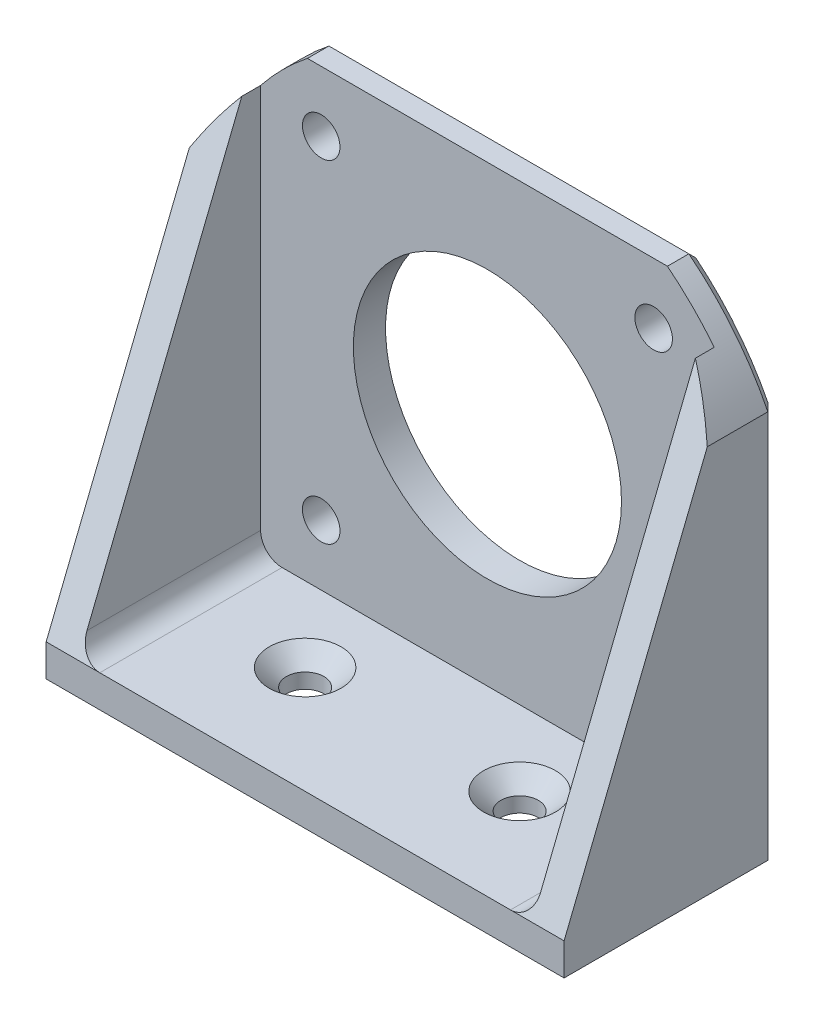
SolidWorks part; units mm, degrees
ref_plane "Front Plane" through (0, 0, 0) normal (0, 0, 1) x (1, 0, 0)
ref_plane "Top Plane" through (0, 0, 0) normal (0, 1, 0) x (1, 0, 0)
ref_plane "Right Plane" through (0, 0, 0) normal (1, 0, 0) x (0, 0, -1)
sketch "Sketch1" plane through (0, 0, 0) normal (0, 1, 0) x (1, 0, 0)
  line L1 (-21.15, 10) -> (21.15, 10) construction
  line L2 (-21.15, 10) -> (-21.15, -10) construction
  line L3 (-21.15, -10) -> (21.15, -10) construction
  line L4 (21.15, 10) -> (21.15, -10) construction
  line L5 (-21.15, 10) -> (21.15, -10) construction
  line L6 (-21.15, -10) -> (21.15, 10) construction
  line L7 (-24.15, 10) -> (24.15, 10)
  line L8 (-24.15, 10) -> (-24.15, -10)
  line L9 (-24.15, -10) -> (24.15, -10)
  line L10 (24.15, 10) -> (24.15, -10)
  line L11 (-24.15, 10) -> (24.15, -10) construction
  line L12 (-24.15, -10) -> (24.15, 10) construction
  point P0 (0, 0)
  point P5 (0, 0)
  dimension "D1" = 20
  dimension "D2" = 42.3
  dimension "D4" = 3
extrude "Boss-Extrude1" add sketch "Sketch1" along normal blind 3
sketch "Sketch2" plane through (0, 3, 0) normal (0, 1, 0) x (1, 0, 0)
  line L0 (24.15, -10) -> (24.15, 10) construction
  line L1 (-24.15, 10) -> (24.15, 10)
  line L2 (-24.15, 10) -> (-24.15, 7)
  line L3 (-24.15, 7) -> (24.15, 7)
  line L4 (24.15, 10) -> (24.15, 7)
  dimension "D1" = 3
extrude "Boss-Extrude2" add sketch "Sketch2" along normal blind 42.3
sketch "Sketch3" plane through (0, 0, -7) normal (0, 0, 1) x (1, 0, 0)
  line L0 (-24.15, 24.15) -> (24.15, 24.15) construction
  line L1 (-24.15, 45.3) -> (-24.15, 3) construction
  line L2 (24.15, 45.3) -> (24.15, 3) construction
  line L4 (-15.5, 39.65) -> (15.5, 39.65) construction
  line L5 (-15.5, 39.65) -> (-15.5, 8.65) construction
  line L6 (-15.5, 8.65) -> (15.5, 8.65) construction
  line L7 (15.5, 39.65) -> (15.5, 8.65) construction
  line L8 (-15.5, 39.65) -> (15.5, 8.65) construction
  line L9 (-15.5, 8.65) -> (15.5, 39.65) construction
  circle A0 centre (0, 24.15) radius 12.5
  circle A1 centre (-15.5, 39.65) radius 1.75
  circle A2 centre (15.5, 39.65) radius 1.75
  circle A3 centre (15.5, 8.65) radius 1.75
  circle A4 centre (-15.5, 8.65) radius 1.75
  point P8 (0, 0)
  point P10 (-15.7944, 8.3556)
  point P11 (0, 0)
  point P13 (0, 0)
  point P14 (0, 0)
  point P22 (0, 24.15)
  dimension "D1" = 25
  dimension "D2" = 3.5
  dimension "D3" = 4
  dimension "D4" = 31
extrude "Cut-Extrude1" cut sketch "Sketch3" against normal through all
sketch "Sketch4" plane through (-24.15, 0, 0) normal (-1, 0, 0) x (0, 0, 1)
  line L0 (-7, 45.3) -> (10, 3)
rib "Rib1" sketch "Sketch4" sketch "Sketch4" thickness 3 extrusion direction parallel to sketch draft on no parameters "D1"=3
mirror "Mirror1" about plane through (0, 0, 0) normal (1, 0, 0) of "Rib1"
sketch "Sketch5" plane through (0, 0, -10) normal (0, 0, -1) x (-1, 0, 0)
  line L0 (-27, 24.15) -> (27, 24.15) construction
  line L1 (-27, 24.15) -> (-32.1021, 24.15)
  line L2 (27, 24.15) -> (32.1021, 24.15)
  arc A0 (27, 24.15) -> (-27, 24.15) centre (0, 24.15) ccw
  arc A1 (32.1021, 24.15) -> (-32.1021, 24.15) centre (0, 24.15) ccw
  dimension "D1" = 54
extrude "Cut-Extrude2" cut sketch "Sketch5" against normal through all
sketch "Sketch6" plane through (0, 3, 0) normal (0, 1, 0) x (1, 0, 0)
  line L0 (-10, -10) -> (-10, 10) construction
  line L1 (-21.15, -10) -> (21.15, -10) construction
  line L2 (16.7833, 10) -> (-16.7833, 10) construction
  line L3 (10, -10) -> (10, 10) construction
  line L4 (-10, 0) -> (10, 0) construction
  circle A0 centre (-10, 0) radius 1.75
  circle A1 centre (10, 0) radius 1.75
  point P14 (-12.0724, -0.1373)
  dimension "D1" = 3.5
  dimension "D2" = 3.5
  dimension "D3" = 20
extrude "Cut-Extrude3" cut sketch "Sketch6" against normal through all
fillet "Fillet1" radius 2 2 edges at (21.15, 3, 1.5) (-21.15, 3, 1.5)
chamfer "Chamfer2" distance 1 angle 45 6 edges at (0, 0, -10) (24.15, 18.1119, -10) (20.9637, 41.1654, -10) (0, 45.3, -10) (-20.9637, 41.1654, -10) (-24.15, 18.1119, -10)
chamfer "Chamfer3" distance 1.6 angle 45 2 edges at (10, 3, 1.75) (-10, 3, 1.75)
